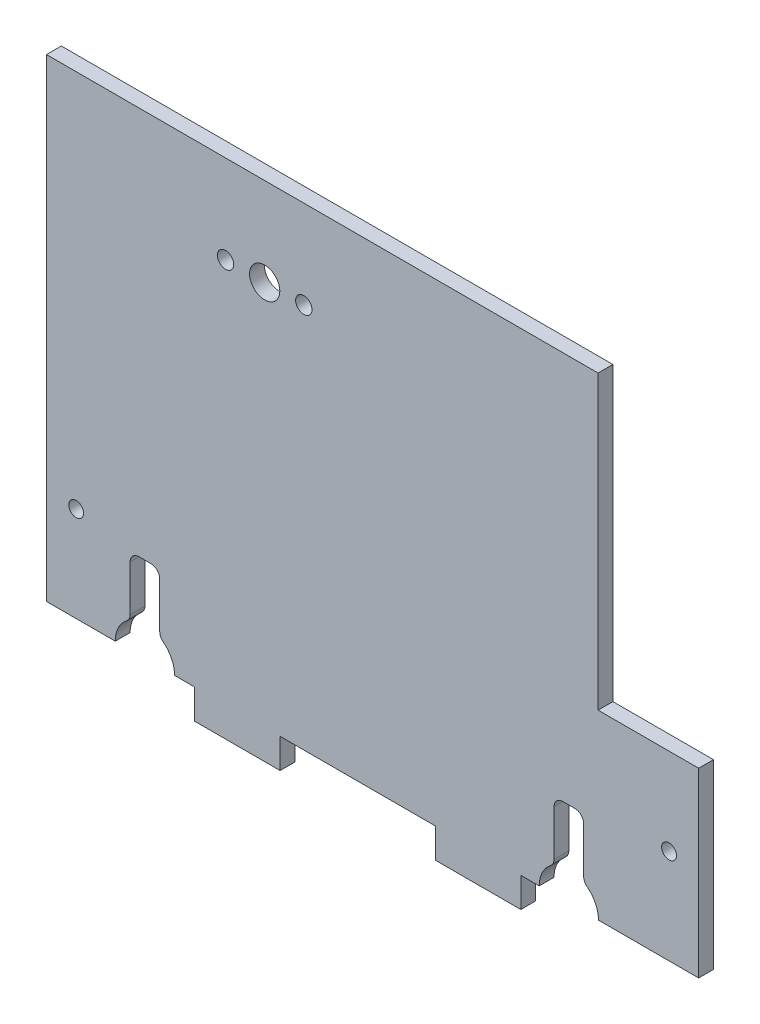
SolidWorks part; units mm, degrees
ref_plane "Front Plane" through (0, 0, 0) normal (0, 0, 1) x (1, 0, 0)
ref_plane "Top Plane" through (0, 0, 0) normal (0, 1, 0) x (1, 0, 0)
ref_plane "Right Plane" through (0, 0, 0) normal (1, 0, 0) x (0, 0, -1)
sketch "Sketch1" plane through (0, 0, 0) normal (0, 0, 1) x (1, 0, 0)
  line L0 (0, 0) -> (-177.8, 0)
  line L1 (-177.8, 0) -> (-177.8, 349.25)
  line L2 (-177.8, 349.25) -> (-25.4, 349.25)
  line L3 (-25.4, 349.25) -> (0, 0)
  dimension "D1" = 349.25
  dimension "D2" = 177.8
  dimension "D3" = 152.4
  dimension "D4" = 0
extrude "Boss-Extrude1" add sketch "Sketch1" along normal blind 3.175
sketch "Sketch2" plane through (0, 0, 3.175) normal (0, 0, 1) x (1, 0, 0)
  line L0 (-177.8, 0) -> (0, 0) construction
  circle A0 centre (-127, 133.35) radius 1.5875
  circle A1 centre (-127, 306.07) radius 1.5875
  dimension "D1" = 3.175
  dimension "D2" = 3.175
  dimension "D3" = 172.72
  dimension "D4" = 172.72
  dimension "D5" = 133.35
  dimension "D6" = 127
extrude "Cut-Extrude1" cut sketch "Sketch2" against normal blind 3.175
sketch "Sketch3" plane through (0, 0, 3.175) normal (0, 0, 1) x (1, 0, 0)
  line L1 (-63.5, 88.9) -> (63.5, 111.2935)
  line L2 (-63.5, 88.9) -> (-63.5, 187.4935)
  line L3 (-63.5, 187.4935) -> (63.5, 187.4935)
  line L4 (63.5, 111.2935) -> (63.5, 187.4935)
  line L5 (-177.8, 0) -> (0, 0) construction
  circle A0 centre (-127, 133.35) radius 1.5875 construction
  dimension "D1" = 127
  dimension "D2" = 76.2
  dimension "D3" = 44.45
  dimension "D4" = 63.5
  dimension "D5" = 10
extrude "Boss-Extrude2" add sketch "Sketch3" against normal blind 3.175
sketch "Sketch4" plane through (0, 0, 3.175) normal (0, 0, 1) x (1, 0, 0)
  line L0 (-44.45, 110.49) -> (-31.9429, 112.6953)
  line L1 (-32.4943, 115.8221) -> (-45.0013, 113.6168)
  line L2 (-45.0013, 113.6168) -> (-44.45, 110.49)
  line L3 (-32.4943, 115.8221) -> (-31.9429, 112.6953)
  line L4 (-6.9288, 117.106) -> (5.5782, 119.3113)
  line L5 (5.0269, 122.4381) -> (-7.4802, 120.2328)
  line L6 (-7.4802, 120.2328) -> (-6.9288, 117.106)
  line L7 (5.0269, 122.4381) -> (5.5782, 119.3113)
  line L8 (-7.1876, 98.8294) -> (63.5, 111.2935) construction
  circle A0 centre (-127, 133.35) radius 1.5875 construction
  dimension "D1" = 3.175
  dimension "D2" = 12.7
  dimension "D3" = 3.175
  dimension "D4" = 12.7
  dimension "D5" = 0
  dimension "D6" = 25.4
  dimension "D7" = 82.55
  dimension "D8" = 22.86
  dimension "D9" = 0
extrude "Cut-Extrude2" cut sketch "Sketch4" against normal blind 3.175
sketch "Sketch5" plane through (0, 0, 3.175) normal (0, 0, 1) x (1, 0, 0)
  line L0 (-127, 133.35) -> (-127, 306.07)
  line L1 (-128.5875, 203.2) -> (-125.4125, 203.2)
  line L2 (-125.4125, 203.2) -> (-125.4125, 215.9)
  line L3 (-125.4125, 215.9) -> (-128.5875, 215.9)
  line L4 (-128.5875, 215.9) -> (-128.5875, 203.2)
  dimension "D1" = 90
  dimension "D2" = 3.175
  dimension "D3" = 1.5875
  dimension "D4" = 69.85
  dimension "D5" = 12.7
extrude "Cut-Extrude3" cut sketch "Sketch5" against normal blind 10.16 contours L2 L3 L0 L1 | L3 L4 L1 L0
pattern_linear "LPattern1" count 2 spacing 25.4 along (0, 1, 0) of "Cut-Extrude3"
sketch "Sketch8" plane through (0, 0, 3.175) normal (0, 0, 1) x (1, 0, 0)
  line L1 (0, 0) -> (-38.1, 0)
  line L2 (0, 0) -> (0, 46.355)
  line L3 (0, 46.355) -> (-38.1, 46.355)
  line L4 (-38.1, 0) -> (-38.1, 46.355)
  dimension "D1" = 38.1
  dimension "D2" = 46.355
extrude "Cut-Extrude6" cut sketch "Sketch8" against normal blind 12.7
sketch "Sketch10" plane through (0, 0, 0) normal (0, 0, -1) x (-1, 0, 0)
  line L1 (177.8, 0) -> (38.1, 0) construction
  circle A0 centre (171.45, 20.32) radius 1.5875
  circle A1 centre (44.45, 20.32) radius 1.5875
  dimension "D1" = 3.175
  dimension "D2" = 20.32
  dimension "D3" = 6.35
  dimension "D4" = 3.175
  dimension "D5" = 20.32
  dimension "D6" = 127
extrude "Cut-Extrude7" cut sketch "Sketch10" against normal blind 7.62
sketch "Sketch11" plane through (0, 0, 0) normal (0, 0, -1) x (-1, 0, 0)
  line L1 (177.8, 0) -> (38.1, 0) construction
  line L3 (62.738, 5.4993) -> (69.088, 5.4993)
  line L4 (62.738, 5.4993) -> (62.738, 18.1993)
  line L5 (62.738, 18.1993) -> (69.088, 18.1993)
  line L6 (69.088, 5.4993) -> (69.088, 18.1993)
  line L7 (153.543, 5.4993) -> (159.893, 5.4993)
  line L8 (153.543, 5.4993) -> (153.543, 18.1993)
  line L9 (153.543, 18.1993) -> (159.893, 18.1993)
  line L10 (159.893, 5.4993) -> (159.893, 18.1993)
  circle A0 centre (156.718, 0) radius 6.35
  circle A1 centre (65.913, 0) radius 6.35
  line M45 (38.1, 0) -> (177.8, 0)
  dimension "D1" = 12.7
  dimension "D2" = 0
  dimension "D3" = 90.805
  dimension "D4" = 12.7
  dimension "D5" = 21.082
  dimension "D6" = 0
  dimension "D7" = 12.7
  dimension "D8" = 3.175
  dimension "D9" = 6.35
  dimension "D10" = 6.35
  dimension "D11" = 3.175
  dimension "D12" = 12.7
extrude "Cut-Extrude8" cut sketch "Sketch11" against normal blind 12.7 contours A1 L6 L5 L4 | A1 L3 M45 | A0 L7 M45 | A0 L10 L9 L8 | L7 A0
fillet "Fillet1" radius 25.4 1 edges at (-38.1, 46.355, 1.5875)
sketch "Sketch13" plane through (0, 0, 0) normal (0, 0, -1) x (-1, 0, 0)
  line L0 (25.4, 349.25) -> (177.8, 349.25) construction
  line L1 (25.4, 349.25) -> (0, 349.25)
  line L2 (25.4, 349.25) -> (25.4, 171.45)
  line L3 (25.4, 171.45) -> (0, 171.45)
  line L4 (0, 349.25) -> (0, 171.45)
  dimension "D1" = 25.4
  dimension "D2" = 0
  dimension "D3" = 177.8
extrude "Boss-Extrude3" add sketch "Sketch13" against normal blind 3.175
pattern_linear "LPattern2" count 2 spacing 76.2 along (0.9848, 0.1736, 0) of "Cut-Extrude2"
sketch "Sketch14" plane through (0, 0, 0) normal (0, 0, -1) x (-1, 0, 0)
  line L0 (150.368, 0) -> (72.263, 0) construction
  line L1 (76.2, 0) -> (95.25, 0)
  line L2 (76.2, 0) -> (76.2, -6.35)
  line L3 (76.2, -6.35) -> (95.25, -6.35)
  line L4 (95.25, 0) -> (95.25, -6.35)
  line L6 (146.05, 0) -> (127, 0)
  line L7 (146.05, 0) -> (146.05, -6.35)
  line L8 (146.05, -6.35) -> (127, -6.35)
  line L9 (127, 0) -> (127, -6.35)
  circle A0 centre (44.45, 20.32) radius 1.5875 construction
  circle A1 centre (171.45, 20.32) radius 1.5875 construction
  dimension "D1" = 6.35
  dimension "D2" = 19.05
  dimension "D3" = 19.05
  dimension "D4" = 6.35
  dimension "D5" = 31.75
  dimension "D6" = 25.4
extrude "Boss-Extrude4" add sketch "Sketch14" against normal blind 3.175
fillet "Fillet2" radius 1.905 8 edges at (-159.893, 18.1993, 1.5875) (-159.893, 5.4993, 1.5875) (-153.543, 18.1993, 1.5875) (-153.543, 5.4993, 1.5875) (-62.738, 5.4993, 1.5875) (-69.088, 5.4993, 1.5875) (-69.088, 18.1993, 1.5875) (-62.738, 18.1993, 1.5875)
sketch "Sketch15" plane through (0, 0, 0) normal (0, 0, -1) x (-1, 0, 0)
  line L0 (38.1, 20.955) -> (38.1, 38.9155)
  line L1 (38.1, 38.9155) -> (59.6461, 38.9155)
  line L2 (59.6461, 38.9155) -> (59.6461, 87.9507)
  line L3 (59.6461, 87.9507) -> (59.6461, 101.4585)
  line L4 (59.6461, 101.4585) -> (177.8, 101.4585)
  line L5 (177.8, 349.25) -> (177.8, 0) construction
  line L6 (177.8, 101.4585) -> (320.9796, 349.25)
  line L7 (320.9796, 349.25) -> (0, 416.8485)
  line L8 (0, 416.8485) -> (-115.4667, 312.7163)
  line L9 (-115.4667, 312.7163) -> (-102.186, 94.7046)
  line L10 (-102.186, 94.7046) -> (38.1, 20.955)
extrude "Cut-Extrude9" cut sketch "Sketch15" against normal through all
sketch "Sketch16" plane through (0, 0, 3.175) normal (0, 0, 1) x (1, 0, 0)
  circle A0 centre (-131.064, 82.55) radius 3.2385
  dimension "D1" = 6.477
extrude "Cut-Extrude10" cut sketch "Sketch16" against normal through all
sketch "Sketch17" plane through (0, 0, 3.175) normal (0, 0, 1) x (1, 0, 0)
  line L0 (-131.064, 82.55) -> (-131.064, 96.9128) construction
  circle A0 centre (-122.682, 82.55) radius 1.75
  circle A1 centre (-139.446, 82.55) radius 1.75
  dimension "D1" = 3.5
  dimension "D2" = 8.382
extrude "Cut-Extrude11" cut sketch "Sketch17" against normal through all
sketch "Sketch18" plane through (0, 0, 0) normal (0, 0, -1) x (-1, 0, 0)
  line L0 (76.2, -6.35) -> (95.25, -6.35) construction
  line L1 (94.488, -6.35) -> (127.762, -6.35)
  line L2 (94.488, -6.35) -> (94.488, 0)
  line L3 (94.488, 0) -> (127.762, 0)
  line L4 (127.762, -6.35) -> (127.762, 0)
  line L5 (127, 0) -> (127, -6.35) construction
  line L6 (95.25, -6.35) -> (95.25, 0) construction
  dimension "D1" = 0.762
  dimension "D2" = 0.762
extrude "Cut-Extrude12" cut sketch "Sketch18" against normal through all
